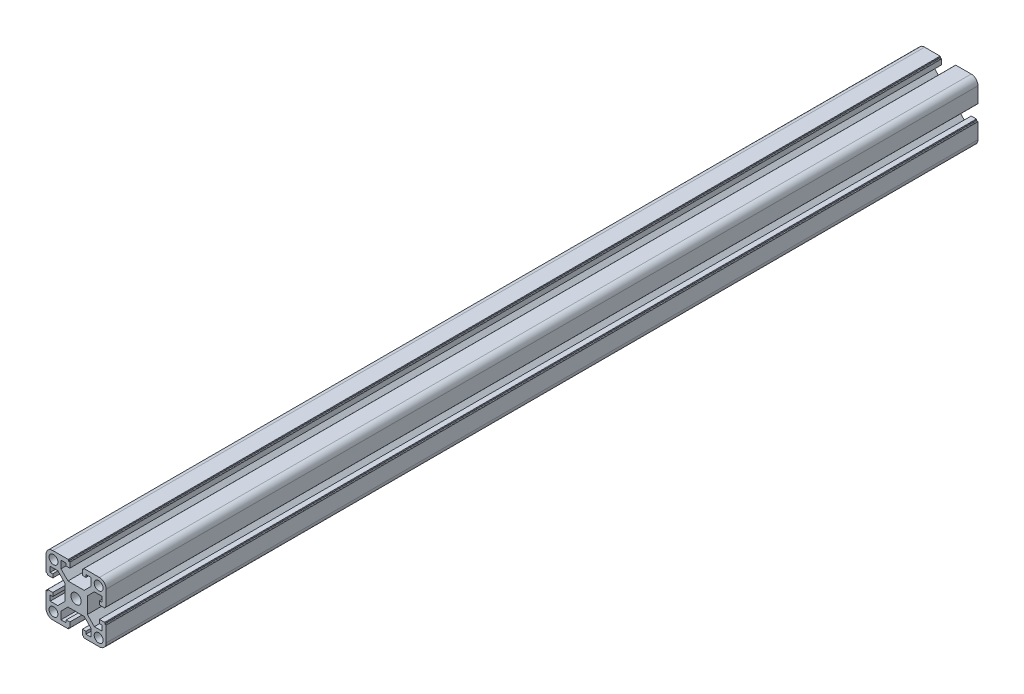
SolidWorks part; units mm, degrees
material "6061-T6 (SS)"
ref_plane "前视基准面" through (0, 0, 0) normal (0, 0, 1) x (1, 0, 0)
ref_plane "上视基准面" through (0, 0, 0) normal (0, 1, 0) x (1, 0, 0)
ref_plane "右视基准面" through (0, 0, 0) normal (1, 0, 0) x (0, 0, -1)
ref_plane "基准面1" through (0, 0, 50) normal (0, 0, 1) x (1, 0, 0)
sketch "草图1" plane through (0, 0, 50) normal (0, 0, 1) x (1, 0, 0)
  line L0 (-1518.245, 3588.0043) -> (-1518.245, 3582.9756)
  line L1 (-1518.245, 3582.9756) -> (-1522.9163, 3578.3043)
  line L2 (-1522.9163, 3578.3043) -> (-1533.6737, 3578.3043)
  line L3 (-1533.6737, 3578.3043) -> (-1538.345, 3582.9756)
  line L4 (-1538.345, 3582.9756) -> (-1538.345, 3588.0043)
  line L5 (-1538.345, 3588.0043) -> (-1534.845, 3588.0043)
  line L6 (-1534.845, 3588.0043) -> (-1534.845, 3586.3043)
  line L7 (-1534.845, 3586.3043) -> (-1532.445, 3586.3043)
  line L8 (-1532.445, 3586.3043) -> (-1532.445, 3589.7043)
  line L9 (-1532.645, 3589.9043) -> (-1533.345, 3589.9043)
  line L10 (-1533.345, 3589.9043) -> (-1533.345, 3590.6043)
  line L11 (-1533.545, 3590.8043) -> (-1543.795, 3590.8043)
  line L12 (-1548.295, 3586.3043) -> (-1548.295, 3576.0543)
  line L13 (-1548.095, 3575.8543) -> (-1547.395, 3575.8543)
  line L14 (-1547.395, 3575.8543) -> (-1547.395, 3575.1543)
  line L15 (-1547.195, 3574.9543) -> (-1543.795, 3574.9543)
  line L16 (-1543.795, 3574.9543) -> (-1543.795, 3577.3543)
  line L17 (-1543.795, 3577.3543) -> (-1545.495, 3577.3543)
  line L18 (-1545.495, 3577.3543) -> (-1545.495, 3580.8543)
  line L19 (-1545.495, 3580.8543) -> (-1540.4663, 3580.8543)
  line L20 (-1540.4663, 3580.8543) -> (-1535.795, 3576.183)
  line L21 (-1535.795, 3576.183) -> (-1535.795, 3565.4256)
  line L22 (-1535.795, 3565.4256) -> (-1540.4663, 3560.7543)
  line L23 (-1540.4663, 3560.7543) -> (-1545.495, 3560.7543)
  line L24 (-1545.495, 3560.7543) -> (-1545.495, 3564.2543)
  line L25 (-1545.495, 3564.2543) -> (-1543.795, 3564.2543)
  line L26 (-1543.795, 3564.2543) -> (-1543.795, 3566.6543)
  line L27 (-1543.795, 3566.6543) -> (-1547.195, 3566.6543)
  line L28 (-1547.395, 3566.4543) -> (-1547.395, 3565.7543)
  line L29 (-1547.395, 3565.7543) -> (-1548.095, 3565.7543)
  line L30 (-1548.295, 3565.5543) -> (-1548.295, 3555.3043)
  line L31 (-1543.795, 3550.8043) -> (-1533.545, 3550.8043)
  line L32 (-1533.345, 3551.0043) -> (-1533.345, 3551.7043)
  line L33 (-1533.345, 3551.7043) -> (-1532.645, 3551.7043)
  line L34 (-1532.445, 3551.9043) -> (-1532.445, 3555.3043)
  line L35 (-1532.445, 3555.3043) -> (-1534.845, 3555.3043)
  line L36 (-1534.845, 3555.3043) -> (-1534.845, 3553.6043)
  line L37 (-1534.845, 3553.6043) -> (-1538.345, 3553.6043)
  line L38 (-1538.345, 3553.6043) -> (-1538.345, 3558.633)
  line L39 (-1538.345, 3558.633) -> (-1533.6737, 3563.3043)
  line L40 (-1533.6737, 3563.3043) -> (-1522.9163, 3563.3043)
  line L41 (-1522.9163, 3563.3043) -> (-1518.245, 3558.633)
  line L42 (-1518.245, 3558.633) -> (-1518.245, 3553.6043)
  line L43 (-1518.245, 3553.6043) -> (-1521.745, 3553.6043)
  line L44 (-1521.745, 3553.6043) -> (-1521.745, 3555.3043)
  line L45 (-1521.745, 3555.3043) -> (-1524.145, 3555.3043)
  line L46 (-1524.145, 3555.3043) -> (-1524.145, 3551.9043)
  line L47 (-1523.945, 3551.7043) -> (-1523.245, 3551.7043)
  line L48 (-1523.245, 3551.7043) -> (-1523.245, 3551.0043)
  line L49 (-1523.045, 3550.8043) -> (-1512.795, 3550.8043)
  line L50 (-1508.295, 3555.3043) -> (-1508.295, 3565.5543)
  line L51 (-1508.495, 3565.7543) -> (-1509.195, 3565.7543)
  line L52 (-1509.195, 3565.7543) -> (-1509.195, 3566.4543)
  line L53 (-1509.395, 3566.6543) -> (-1512.795, 3566.6543)
  line L54 (-1512.795, 3566.6543) -> (-1512.795, 3564.2543)
  line L55 (-1512.795, 3564.2543) -> (-1511.095, 3564.2543)
  line L56 (-1511.095, 3564.2543) -> (-1511.095, 3560.7543)
  line L57 (-1511.095, 3560.7543) -> (-1516.1237, 3560.7543)
  line L58 (-1516.1237, 3560.7543) -> (-1520.795, 3565.4256)
  line L59 (-1520.795, 3565.4256) -> (-1520.795, 3576.183)
  line L60 (-1520.795, 3576.183) -> (-1516.1237, 3580.8543)
  line L61 (-1516.1237, 3580.8543) -> (-1511.095, 3580.8543)
  line L62 (-1511.095, 3580.8543) -> (-1511.095, 3577.3543)
  line L63 (-1511.095, 3577.3543) -> (-1512.795, 3577.3543)
  line L64 (-1512.795, 3577.3543) -> (-1512.795, 3574.9543)
  line L65 (-1512.795, 3574.9543) -> (-1509.395, 3574.9543)
  line L66 (-1509.195, 3575.1543) -> (-1509.195, 3575.8543)
  line L67 (-1509.195, 3575.8543) -> (-1508.495, 3575.8543)
  line L68 (-1508.295, 3576.0543) -> (-1508.295, 3586.3043)
  line L69 (-1512.795, 3590.8043) -> (-1523.045, 3590.8043)
  line L70 (-1523.245, 3590.6043) -> (-1523.245, 3589.9043)
  line L71 (-1523.245, 3589.9043) -> (-1523.945, 3589.9043)
  line L72 (-1524.145, 3589.7043) -> (-1524.145, 3586.3043)
  line L73 (-1524.145, 3586.3043) -> (-1521.745, 3586.3043)
  line L74 (-1521.745, 3586.3043) -> (-1521.745, 3588.0043)
  line L75 (-1521.745, 3588.0043) -> (-1518.245, 3588.0043)
  circle A0 centre (-1513.27, 3555.7793) radius 2.95
  circle A1 centre (-1528.295, 3570.8043) radius 3.4
  circle A2 centre (-1513.27, 3585.8293) radius 2.95
  arc A3 (-1532.445, 3589.7043) -> (-1532.645, 3589.9043) centre (-1532.645, 3589.7043) ccw
  arc A4 (-1533.345, 3590.6043) -> (-1533.545, 3590.8043) centre (-1533.545, 3590.6043) ccw
  arc A5 (-1543.795, 3590.8043) -> (-1548.295, 3586.3043) centre (-1543.795, 3586.3043) ccw
  arc A6 (-1548.295, 3576.0543) -> (-1548.095, 3575.8543) centre (-1548.095, 3576.0543) ccw
  arc A7 (-1547.395, 3575.1543) -> (-1547.195, 3574.9543) centre (-1547.195, 3575.1543) ccw
  arc A8 (-1547.195, 3566.6543) -> (-1547.395, 3566.4543) centre (-1547.195, 3566.4543) ccw
  arc A9 (-1548.095, 3565.7543) -> (-1548.295, 3565.5543) centre (-1548.095, 3565.5543) ccw
  arc A10 (-1548.295, 3555.3043) -> (-1543.795, 3550.8043) centre (-1543.795, 3555.3043) ccw
  arc A11 (-1533.545, 3550.8043) -> (-1533.345, 3551.0043) centre (-1533.545, 3551.0043) ccw
  arc A12 (-1532.645, 3551.7043) -> (-1532.445, 3551.9043) centre (-1532.645, 3551.9043) ccw
  arc A13 (-1524.145, 3551.9043) -> (-1523.945, 3551.7043) centre (-1523.945, 3551.9043) ccw
  arc A14 (-1523.245, 3551.0043) -> (-1523.045, 3550.8043) centre (-1523.045, 3551.0043) ccw
  arc A15 (-1512.795, 3550.8043) -> (-1508.295, 3555.3043) centre (-1512.795, 3555.3043) ccw
  arc A16 (-1508.295, 3565.5543) -> (-1508.495, 3565.7543) centre (-1508.495, 3565.5543) ccw
  arc A17 (-1509.195, 3566.4543) -> (-1509.395, 3566.6543) centre (-1509.395, 3566.4543) ccw
  arc A18 (-1509.395, 3574.9543) -> (-1509.195, 3575.1543) centre (-1509.395, 3575.1543) ccw
  arc A19 (-1508.495, 3575.8543) -> (-1508.295, 3576.0543) centre (-1508.495, 3576.0543) ccw
  arc A20 (-1508.295, 3586.3043) -> (-1512.795, 3590.8043) centre (-1512.795, 3586.3043) ccw
  arc A21 (-1523.045, 3590.8043) -> (-1523.245, 3590.6043) centre (-1523.045, 3590.6043) ccw
  arc A22 (-1523.945, 3589.9043) -> (-1524.145, 3589.7043) centre (-1523.945, 3589.7043) ccw
  circle A23 centre (-1543.32, 3585.8293) radius 2.95
  circle A24 centre (-1543.32, 3555.7793) radius 2.95
extrude "凸台-拉伸1" add sketch "草图1" against normal mid plane 580
ref_plane "基准面2" through (-1528.295, 0, 0) normal (1, 0, 0) x (0, 0, -1)
ref_plane "基准面3" through (0, 3570.8043, 0) normal (0, 1, 0) x (1, 0, 0)
